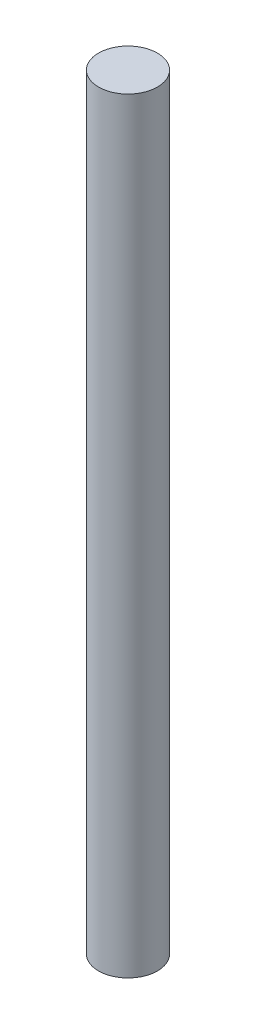
SolidWorks part; units mm, degrees
ref_plane "Front Plane" through (0, 0, 0) normal (0, 0, 1) x (1, 0, 0)
ref_plane "Top Plane" through (0, 0, 0) normal (0, 1, 0) x (1, 0, 0)
ref_plane "Right Plane" through (0, 0, 0) normal (1, 0, 0) x (0, 0, -1)
sketch "Sketch1" plane through (0, 0, 0) normal (0, 1, 0) x (1, 0, 0)
  circle A0 centre (0, 0) radius 152.4
extrude "Boss-Extrude1" add sketch "Sketch1" along normal blind 3962.4
sketch "Sketch2" plane through (0, 3962.4, 0) normal (0, 1, 0) x (1, 0, 0)
  line L0 (0, 152.4) -> (0, -152.4)
  circle A0 centre (0, 0) radius 152.4 construction
sketch "Sketch3" plane through (0, 0, 0) normal (0, -1, 0) x (1, 0, 0)
  line L0 (0, -152.4) -> (0, 152.4)
  circle A0 centre (0, 0) radius 152.4 construction
sketch "Sketch4" plane through (0, 0, 0) normal (0, -1, 0) x (-1, 0, 0)
  line L0 (-152.4, 0) -> (152.4, 0)
  circle A0 centre (0, 0) radius 152.4 construction
sketch "Sketch5" plane through (0, 3962.4, 0) normal (0, 1, 0) x (1, 0, 0)
  line L0 (-152.4, 0) -> (152.4, 0)
  circle A0 centre (0, 0) radius 152.4 construction
